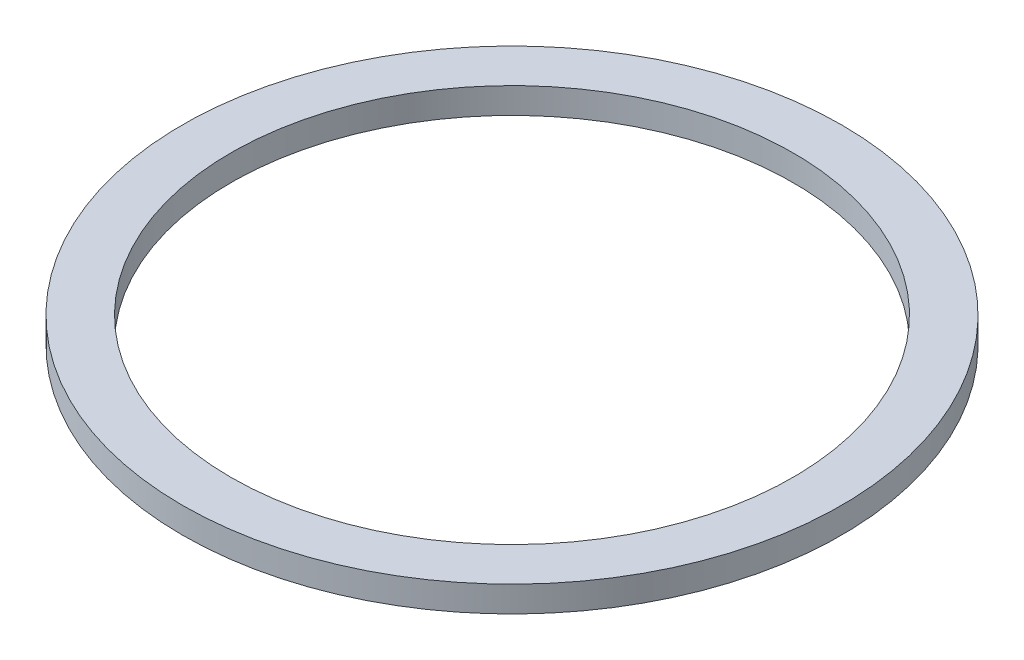
SolidWorks part; units mm, degrees
ref_plane "Front Plane" through (0, 0, 0) normal (0, 0, 1) x (1, 0, 0)
ref_plane "Top Plane" through (0, 0, 0) normal (0, 1, 0) x (1, 0, 0)
ref_plane "Right Plane" through (0, 0, 0) normal (1, 0, 0) x (0, 0, -1)
sketch "Sketch1" plane through (0, 0, 0) normal (0, 1, 0) x (1, 0, 0)
  circle A0 centre (0, 0) radius 10.2
  circle A1 centre (0, 0) radius 8.7
  dimension "D1" = 17.4
  dimension "D2" = 1.5
extrude "Boss-Extrude1" add sketch "Sketch1" along normal blind 0.8
